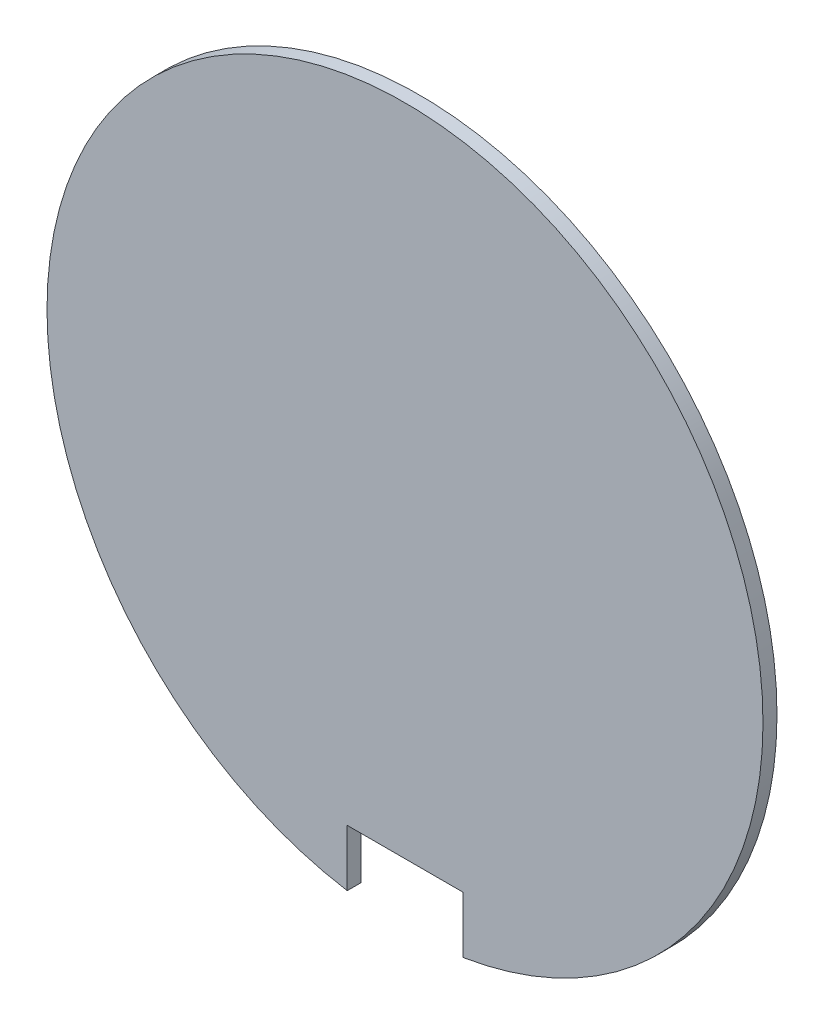
SolidWorks part; units mm, degrees
ref_plane "FRONT" through (0, 0, 0) normal (0, 0, 1) x (1, 0, 0)
ref_plane "TOP" through (0, 0, 0) normal (0, 1, 0) x (1, 0, 0)
ref_plane "SIDE" through (0, 0, 0) normal (1, 0, 0) x (0, 0, -1)
sketch "Sketch1" plane through (0, 0, 0) normal (0, 0, 1) x (1, 0, 0)
  line L3 (1.6764, -10.2524) -> (1.6764, -8.6106)
  line L4 (1.6764, -8.6106) -> (-1.6764, -8.6106)
  line L5 (-1.6764, -8.6106) -> (-1.6764, -10.2524)
  line L6 (1.6764, -10.2524) -> (1.6764, -8.6106)
  line L7 (1.6764, -8.6106) -> (-1.6764, -8.6106)
  line L8 (-1.6764, -8.6106) -> (-1.6764, -10.2524)
  arc A1 (1.6764, -10.2524) -> (-1.6764, -10.2524) centre (0, 0) ccw
  arc A2 (1.6764, -10.2524) -> (-1.6764, -10.2524) centre (0, 0) ccw
  dimension "D1" = 0.4064
extrude "Base-Extrude" add sketch "Sketch1" along normal blind 0.4064
